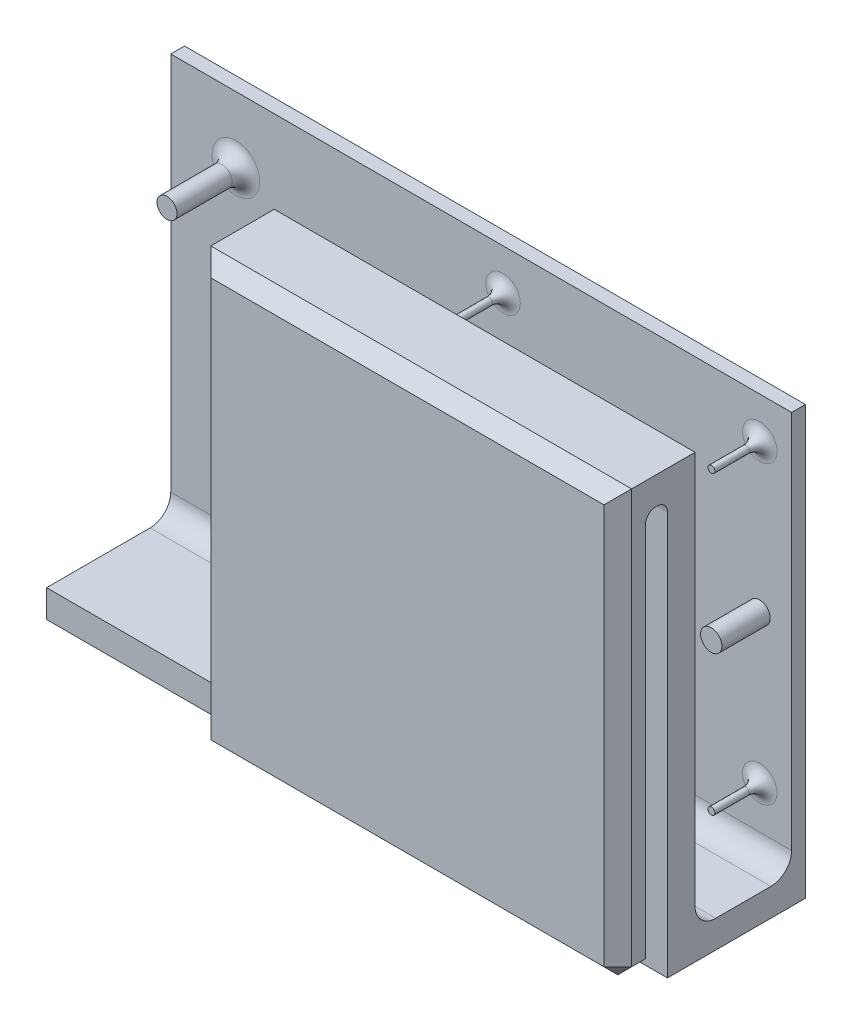
SolidWorks part; units mm, degrees
ref_plane "Front Plane" through (0, 0, 0) normal (0, 0, 1) x (1, 0, 0)
ref_plane "Top Plane" through (0, 0, 0) normal (0, 1, 0) x (1, 0, 0)
ref_plane "Right Plane" through (0, 0, 0) normal (1, 0, 0) x (0, 0, -1)
sketch "Sketch1" plane through (0, 0, 0) normal (1, 0, 0) x (0, 0, -1)
  line L0 (0, 30) -> (0, -30)
  line L1 (0, -30) -> (18, -30)
  line L2 (18, -30) -> (18, 30)
  line L3 (0, 30) -> (-7.2, 30)
  line L4 (-7.2, 30) -> (-7.2, -30)
  point P4 (0, 0)
  point P9 (0, 0)
  dimension "D1" = 18
  dimension "D2" = 60
  dimension "D3" = 7.2
extrude "Extrude-Thin1" add sketch "Sketch1" against normal blind 90 thin thin type mid plane wall 4
sketch "Sketch2" plane through (0, 32, 0) normal (0, 1, 0) x (1, 0, 0)
  line L0 (-90, -9.2) -> (0, -9.2) construction
  line L1 (-90, 2) -> (-61, 2)
  line L2 (-90, 2) -> (-90, -9.2)
  line L3 (-90, -9.2) -> (-61, -9.2)
  line L4 (-61, 2) -> (-61, -9.2)
  dimension "D1" = 29
extrude "Cut-Extrude1" cut sketch "Sketch2" against normal up to surface (60 mm away) up to face at (-45, -28, -9)
sketch "Sketch3" plane through (0, -28, 0) normal (0, 1, 0) x (1, 0, 0)
  line L4 (-61, -5.2) -> (-90, -5.2)
  line L5 (-90, -5.2) -> (-90, -9.2)
  line L6 (-90, -9.2) -> (-61, -9.2)
  line L7 (-61, -9.2) -> (-61, -5.2)
  line L8 (-61, -5.2) -> (-90, -5.2)
  line L9 (-90, -5.2) -> (-90, -9.2)
  line L10 (-90, -9.2) -> (-61, -9.2)
  line L11 (-61, -9.2) -> (-61, -5.2)
  dimension "D1" = 0
extrude "Cut-Extrude2" cut sketch "Sketch3" against normal through all
sketch "Sketch4" plane through (0, 0, -16) normal (0, 0, 1) x (1, 0, 0)
  line L2 (-90, 30) -> (0, 30) construction
  line L3 (-88, 28) -> (-45, 28) construction
  line L4 (-88, 28) -> (-88, -12.5) construction
  line L5 (-88, -12.5) -> (-45, -12.5) construction
  line L6 (-45, 28) -> (-45, -12.5) construction
  line L7 (-90, 30) -> (-90, -28) construction
  circle A0 centre (-80.55, 20.4) radius 1.45
  circle A1 centre (-52.4, -5.2) radius 1.4
  point P2 (-52.4, -6.6)
  point P3 (-51, -5.2)
  point P4 (-80.55, 21.85)
  point P5 (-79.1, 20.4)
  point P12 (-82, 20.4)
  dimension "D3" = 2.9
  dimension "D9" = 2.8
  dimension "D2" = 6.15
  dimension "D4" = 43
  dimension "D5" = 40.5
  dimension "D6" = 6
  dimension "D7" = 5.9
  dimension "D8" = 2
  dimension "D10" = 2
  dimension "D11" = 6
extrude "Boss-Extrude1" add sketch "Sketch4" along normal blind 10
sketch "Sketch5" plane through (0, 0, 9.2) normal (0, 0, 1) x (1, 0, 0)
  line L1 (-50.6671, 26.844) -> (-8.3671, 26.844) construction
  line L2 (-50.6671, 26.844) -> (-50.6671, 2.844) construction
  line L3 (-50.6671, 2.844) -> (-8.3671, 2.844) construction
  line L4 (-8.3671, 26.844) -> (-8.3671, 2.844) construction
  point P4 (-50.6671, 26.844)
  dimension "D1" = 42.3
  dimension "D2" = 24
fillet "Fillet1" radius 3 2 edges at (-30.5, -28, -2) (-45, -28, -16)
chamfer "Chamfer1" distance 2 angle 45 10 edges at (-45, -32, -20) (-90, -1, -20) (0, -1, -20) (-45, 30, -20) (0, 1, 9.2) (-30.5, 32, 9.2) (-61, 1, 9.2) (0, -30, 7.2) (-30.5, -30, 9.2) (-61, -30, 7.2)
sketch "Sketch6" plane through (0, 0, -16) normal (0, 0, 1) x (1, 0, 0)
  line L0 (-45.45, 2.6) -> (-1, 2.6) construction
  line L1 (-45.45, 28) -> (-1, 28) construction
  line L2 (-45.45, 28) -> (-45.45, -22.8) construction
  line L3 (-45.45, -22.8) -> (-1, -22.8) construction
  line L4 (-1, 28) -> (-1, -22.8) construction
  line L5 (-23.225, 28) -> (-23.225, -22.8) construction
  line L6 (0, 30) -> (0, -25) construction
  line L7 (-90, 30) -> (0, 30) construction
  circle A0 centre (-41.83, 24.05) radius 0.5
  circle A1 centre (-41.83, -18.85) radius 0.5
  circle A2 centre (-41.8, 2.6) radius 1.55
  circle A3 centre (-4.62, -18.85) radius 0.5
  circle A4 centre (-4.65, 2.6) radius 1.55
  circle A5 centre (-4.62, 24.05) radius 0.5
  point P8 (-41.83, -18.35)
  point P9 (-41.83, 23.55)
  point P12 (-43.35, 2.6)
  point P23 (-42.33, 24.05)
  dimension "D3" = 1
  dimension "D5" = 1
  dimension "D7" = 3.1
  dimension "D1" = 44.45
  dimension "D2" = 50.8
  dimension "D4" = 41.9
  dimension "D6" = 2.1
  dimension "D8" = 1
  dimension "D9" = 2
  dimension "D10" = 3.12
extrude "Boss-Extrude2" add sketch "Sketch6" along normal blind 7
fillet "Fillet2" radius 2 6 edges at (-51, -5.2, -16) (-79.1, 20.4, -16) (-41.33, -18.85, -16) (-5.12, -18.85, -16) (-5.12, 24.05, -16) (-41.33, 24.05, -16)
fillet "Fillet3" radius 1.5 2 edges at (-30.5, 28, 5.2) (-30.5, 28, 2)
